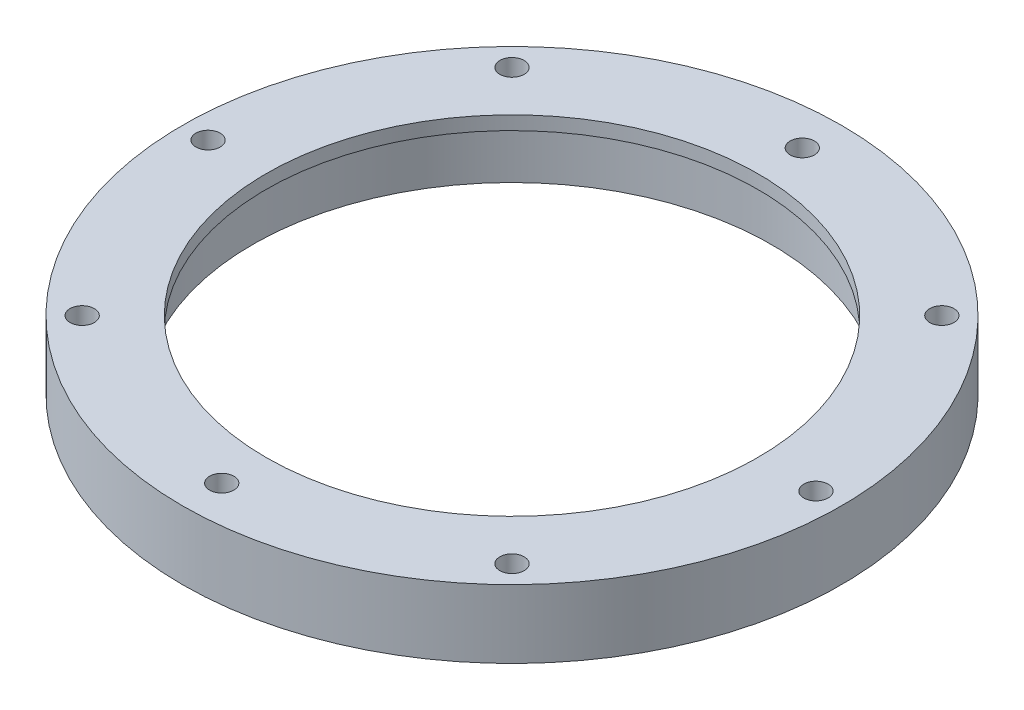
SolidWorks part; units mm, degrees
material "1060 合金"
ref_plane "前视基准面" through (0, 0, 0) normal (0, 0, 1) x (1, 0, 0)
ref_plane "上视基准面" through (0, 0, 0) normal (0, 1, 0) x (1, 0, 0)
ref_plane "右视基准面" through (0, 0, 0) normal (1, 0, 0) x (0, 0, -1)
other "Configuration Table"
sketch "草图1" plane through (0, 0, 0) normal (0, 1, 0) x (1, 0, 0)
  circle A0 centre (0, 0) radius 38
  circle A1 centre (0, 0) radius 48.25
  dimension "D1" = 76
  dimension "D2" = 96.5
extrude "凸台-拉伸1" add sketch "草图1" along normal blind 10
sketch "草图2" plane through (0, 10, 0) normal (0, 1, 0) x (1, 0, 0)
  circle A0 centre (0, 0) radius 38
  circle A1 centre (0, 0) radius 38 construction
  circle A2 centre (0, 0) radius 36
  dimension "D1" = 72
extrude "凸台-拉伸2" add sketch "草图2" against normal blind 2
sketch "草图3" plane through (0, 0, 0) normal (0, -1, 0) x (1, 0, 0)
  circle A0 centre (0, 0) radius 44.5 construction
  circle A1 centre (0, 44.5) radius 1.775
  circle A2 centre (31.4663, 31.4663) radius 1.775
  circle A3 centre (44.5, 0) radius 1.775
  circle A4 centre (31.4663, -31.4663) radius 1.775
  circle A5 centre (0, -44.5) radius 1.775
  circle A6 centre (-31.4663, -31.4663) radius 1.775
  circle A7 centre (-44.5, 0) radius 1.775
  circle A8 centre (-31.4663, 31.4663) radius 1.775
  point P21 (0, 0)
  dimension "D1" = 89
  dimension "D2" = 3.55
  dimension "D3" = 8
extrude "切除-拉伸1" cut sketch "草图3" against normal through all both and the other way through all
sketch "草图4" plane through (0, 10, 0) normal (0, 1, 0) x (1, 0, 0)
  circle A0 centre (0, -44.5) radius 2
  circle A1 centre (0, 44.5) radius 2
  dimension "D1" = 4
extrude "凸台-拉伸3" add sketch "草图4" against normal up to surface (10 mm away) up to face at (0, 0, 46.275)
sketch "草图5" plane through (0, 10, 0) normal (0, 1, 0) x (1, 0, 0)
  circle A0 centre (0.0001, -42.5001) radius 1.775
  circle A2 centre (0, 42.5) radius 1.775
  circle A3 centre (0.0001, -42.5001) radius 1.775 construction
  arc A4 (1.0253, 43.5253) -> (-1.0253, 41.4747) centre (0, 42.5) ccw construction
  dimension "D1" = 3.55
extrude "切除-拉伸2" cut sketch "草图5" against normal up to surface (10 mm away) up to face at (31.4663, 0, 33.2413)
